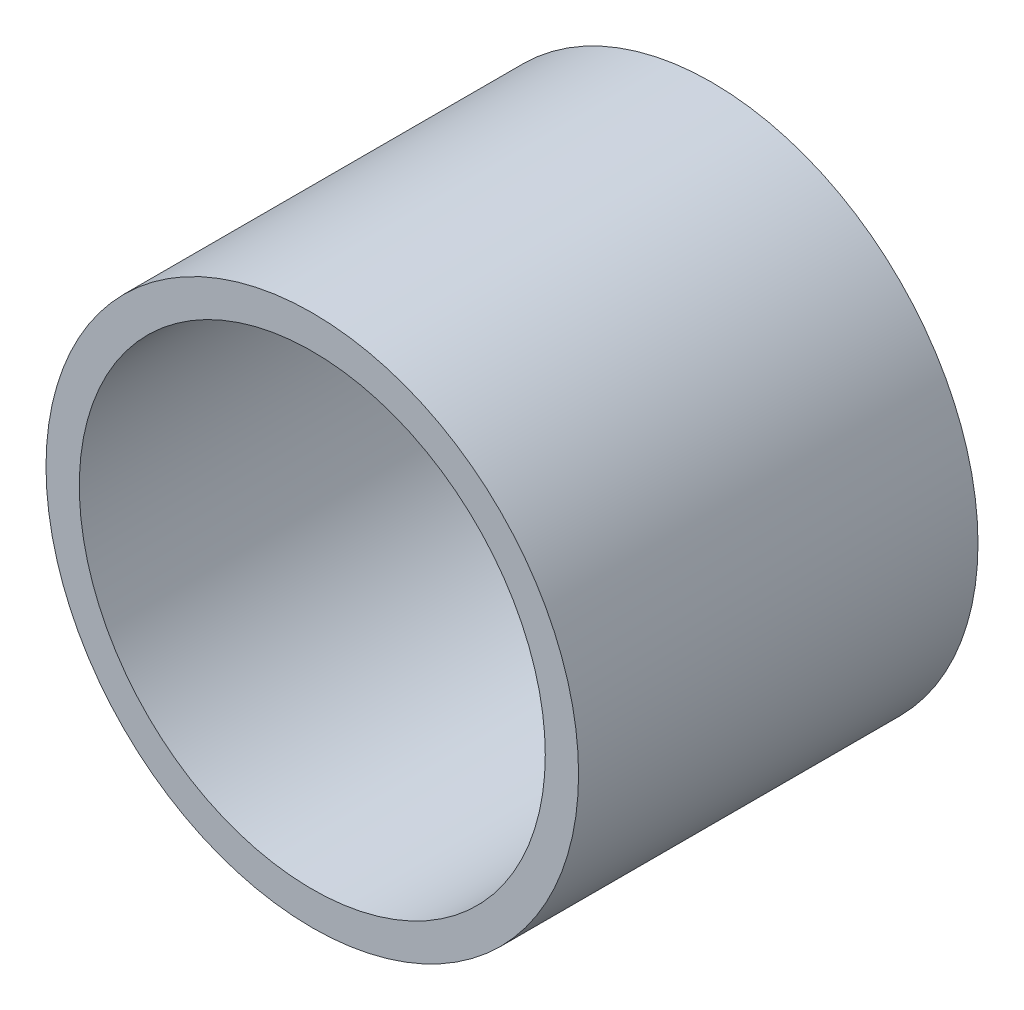
SolidWorks part; units mm, degrees
ref_plane "Front Plane" through (0, 0, 0) normal (0, 0, 1) x (1, 0, 0)
ref_plane "Top Plane" through (0, 0, 0) normal (0, 1, 0) x (1, 0, 0)
ref_plane "Right Plane" through (0, 0, 0) normal (1, 0, 0) x (0, 0, -1)
sketch "Sketch1" plane through (0, 0, 0) normal (0, 0, 1) x (1, 0, 0)
  circle A0 centre (0, 0) radius 3.5
  circle A1 centre (0, 0) radius 4
  dimension "D1" = 7
  dimension "D2" = 8
extrude "Boss-Extrude1" add sketch "Sketch1" along normal blind 6
